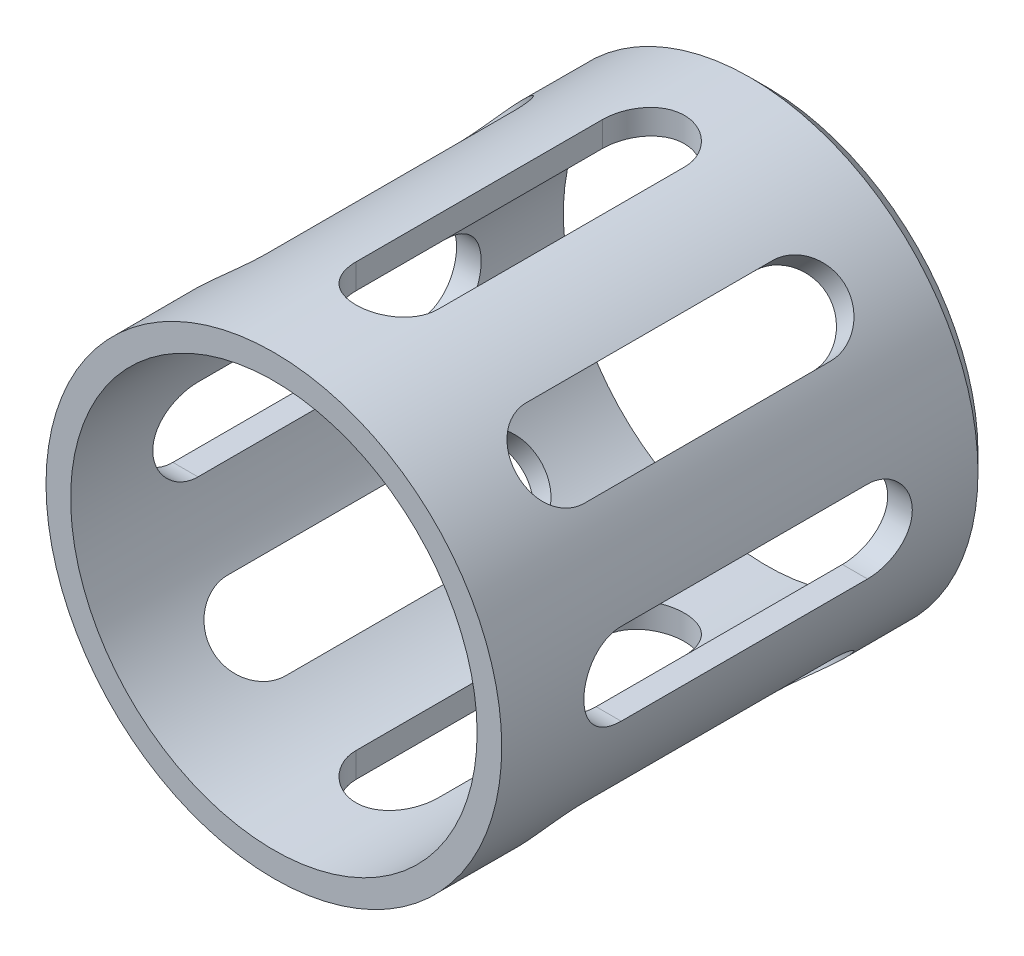
SolidWorks part; units mm, degrees
ref_plane "Front Plane" through (0, 0, 0) normal (0, 0, 1) x (1, 0, 0)
ref_plane "Top Plane" through (0, 0, 0) normal (0, 1, 0) x (1, 0, 0)
ref_plane "Right Plane" through (0, 0, 0) normal (1, 0, 0) x (0, 0, -1)
sketch "Sketch1" plane through (0, 0, 0) normal (0, 0, 1) x (1, 0, 0)
  circle A0 centre (0, 0) radius 24.75
  circle A1 centre (0, 0) radius 27.75
  dimension "D1" = 49.5
  dimension "D2" = 55.5
extrude "Boss-Extrude1" add sketch "Sketch1" along normal blind 60
sketch "Sketch2" plane through (0, 0, 0) normal (1, 0, 0) x (0, 0, -1)
  line L0 (-3.8303, 0) -> (-83.5441, 0) construction
  line L1 (-10, -5) -> (-10, 5)
  line L2 (-10, 5) -> (-50, 5)
  line L3 (-30, 0) -> (-30, 28.25) construction
  line L4 (-50, -5) -> (-50, 5)
  line L6 (0, -27.75) -> (0, 27.75) construction
  line L7 (-10, -5) -> (-50, -5)
  line L8 (-45, 0) -> (-45, 5) construction
  circle A0 centre (-50, 0) radius 5 construction
  arc A1 (-45, 5) -> (-45, -5) centre (-45, 0) ccw
  arc A2 (-15, 5) -> (-15, -5) centre (-15, 0) cw
  point P13 (-30, 5)
  point P15 (-10, 0)
  point P16 (-50, 0)
  dimension "D1" = 20
  dimension "D2" = 10
  dimension "D3" = 5
extrude "Cut-Extrude1" cut sketch "Sketch2" against normal through all both and the other way through all
pattern_circular "CirPattern1" count 8 over 360 about axis through (0, 0, 0) along (0, 0, 1) of "Cut-Extrude1"
chamfer "Chamfer1" distance 2 angle 45 1 edges at (27.75, 0, 0)
